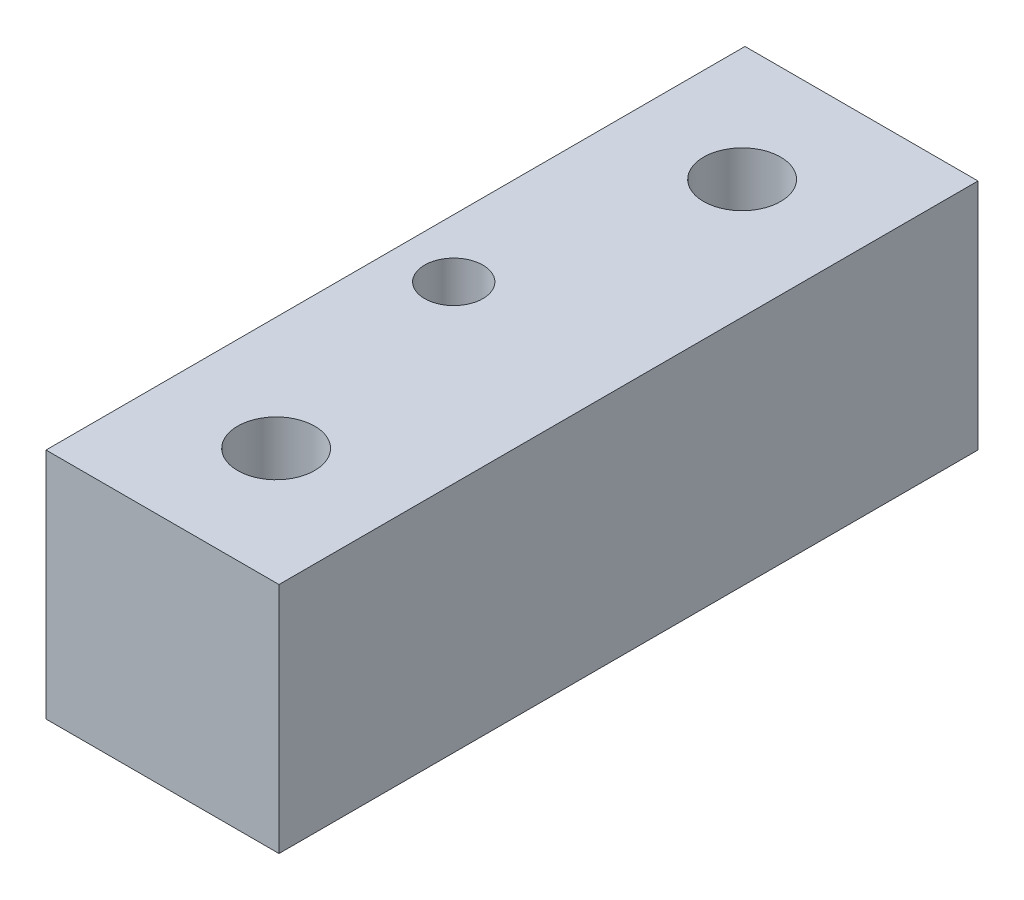
SolidWorks part; units mm, degrees
material "6061 Alloy"
ref_plane "Front Plane" through (0, 0, 0) normal (0, 0, 1) x (1, 0, 0)
ref_plane "Top Plane" through (0, 0, 0) normal (0, 1, 0) x (1, 0, 0)
ref_plane "Right Plane" through (0, 0, 0) normal (1, 0, 0) x (0, 0, -1)
sketch "Sketch1" plane through (0, 0, 0) normal (0, 0, 1) x (1, 0, 0)
  line L1 (0, 0) -> (12.7, 0)
  line L2 (0, 0) -> (0, 12.7)
  line L3 (0, 12.7) -> (12.7, 12.7)
  line L4 (12.7, 0) -> (12.7, 12.7)
  dimension "D1" = 12.7
  dimension "D2" = 12.7
extrude "Boss-Extrude1" add sketch "Sketch1" along normal blind 38.1
hole_wizard "Tap Drill for M5x0.8 Tap1" positions "Sketch5" profile "Sketch4" hole size "M5x0.8" standard "ANSI Metric" end condition through all
sketch "Sketch5" plane through (0, 12.7, 0) normal (0, 1, 0) x (1, 0, 0)
  line L0 (12.7, -38.1) -> (0, -38.1) construction
  line L1 (12.7, 0) -> (0, 0) construction
  point P0 (6.1933, -6.35)
  point P2 (6.1933, -31.75)
  dimension "D1" = 6.35
  dimension "D2" = 6.35
sketch "Sketch4" plane through (6.1933, 12.7, 6.35) normal (1, 0, 0) x (0, 0, 1)
  line L0 (0, 0) -> (0, 12.7)
  line L1 (0, 12.7) -> (2.1, 12.7)
  line L2 (2.1, 12.7) -> (2.1, 0)
  line L5 (2.1, 0) -> (0, 0)
  line L11 (0, -6.35) -> (0, 107.95) construction
  dimension "Thru Hole Dia." = 4.2
  dimension "Thru Hole Depth" = 12.7
hole_wizard "1/8 (0.125) Diameter Hole1" positions "Sketch3" profile "Sketch2" hole size "1/8" standard "ANSI Inch" end condition through all
sketch "Sketch3" plane through (0, 12.7, 0) normal (0, 1, 0) x (1, 0, 0)
  line L1 (12.7, -38.1) -> (12.7, 0) construction
  line L3 (0, -38.1) -> (0, 0) construction
  point P0 (3.175, -19.05)
  point P10 (12.7, -19.05)
  dimension "D1" = 3.175
sketch "Sketch2" plane through (3.175, 12.7, 19.05) normal (1, 0, 0) x (0, 0, 1)
  line L0 (0, 0) -> (0, 12.7)
  line L1 (0, 12.7) -> (1.5875, 12.7)
  line L2 (1.5875, 12.7) -> (1.5875, 0)
  line L5 (1.5875, 0) -> (0, 0)
  line L11 (0, -6.35) -> (0, 107.95) construction
  dimension "Thru Hole Dia." = 3.175
  dimension "Thru Hole Depth" = 12.7
